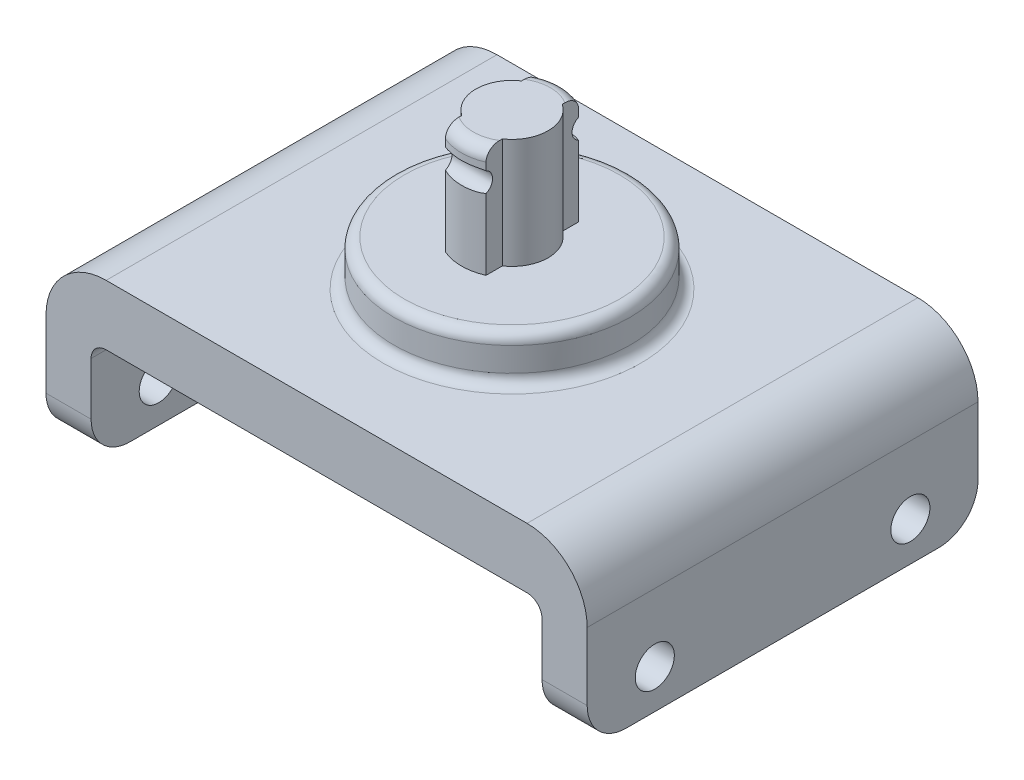
SolidWorks part; units mm, degrees
ref_plane "Front Plane" through (0, 0, 0) normal (0, 0, 1) x (1, 0, 0)
ref_plane "Top Plane" through (0, 0, 0) normal (0, 1, 0) x (1, 0, 0)
ref_plane "Right Plane" through (0, 0, 0) normal (1, 0, 0) x (0, 0, -1)
sketch "Sketch1" plane through (0, 0, 0) normal (0, 0, 1) x (1, 0, 0)
  line L0 (-18, 11.1) -> (18, 11.1)
  line L1 (18, 11.1) -> (18, 0)
  line L2 (18, 0) -> (15, 0)
  line L3 (15, 0) -> (15, 7.1)
  line L4 (15, 7.1) -> (-15, 7.1)
  line L5 (-15, 7.1) -> (-15, 0)
  line L6 (-15, 0) -> (-18, 0)
  line L7 (-18, 0) -> (-18, 11.1)
  line L8 (-15, 0) -> (15, 0) construction
  dimension "D1" = 3
  dimension "D2" = 30
  dimension "D3" = 4
  dimension "D4" = 7.1
extrude "Boss-Extrude1" add sketch "Sketch1" along normal mid plane 26
sketch "Sketch2" plane through (18, 0, 0) normal (1, 0, 0) x (0, 0, -1)
  line L0 (-13, 0) -> (13, 0) construction
  line L1 (-8.5, 2.6) -> (8.5, 2.6) construction
  line L2 (0, 2.6) -> (0, 0) construction
  circle A0 centre (-8.5, 2.6) radius 1.3
  circle A1 centre (8.5, 2.6) radius 1.3
  dimension "D2" = 2.6
  dimension "D1" = 2.6
  dimension "D3" = 17
extrude "Cut-Extrude1" cut sketch "Sketch2" against normal through all
fillet "Fillet1" radius 1 2 edges at (-15, 7.1, 0) (15, 7.1, 0)
fillet "Fillet2" radius 2.6 4 edges at (16.5, 0, 13) (-16.5, 0, 13) (-16.5, 0, -13) (16.5, 0, -13)
fillet "Fillet3" radius 4 2 edges at (18, 11.1, 0) (-18, 11.1, 0)
sketch "Sketch3" plane through (0, 11.1, 0) normal (0, 1, 0) x (1, 0, 0)
  circle A0 centre (0, 0) radius 7.86
  dimension "D1" = 15.72
extrude "Boss-Extrude2" add sketch "Sketch3" along normal blind 3
fillet "Fillet4" radius 0.7 2 edges at (0, 14.1, 7.86) (0, 11.1, -7.86)
sketch "Sketch5" plane through (0, 14.1, 0) normal (0, 1, 0) x (1, 0, 0)
  line L0 (1.35, 1.9904) -> (1.35, 3.0769)
  line L2 (-1.35, -3.0769) -> (-1.35, -1.9904)
  line L4 (1.35, -3.0769) -> (1.35, -1.9904)
  line L7 (-1.35, 1.9904) -> (-1.35, 3.0769)
  arc A0 (-1.35, 1.9904) -> (-1.35, -1.9904) centre (0, 0) ccw
  arc A1 (1.35, -1.9904) -> (1.35, 1.9904) centre (0, 0) ccw
  arc A2 (-1.35, -3.0769) -> (1.35, -3.0769) centre (0, 0) ccw
  arc A3 (1.35, 3.0769) -> (-1.35, 3.0769) centre (0, 0) ccw
  dimension "D1" = 4.81
  dimension "D3" = 6.72
  dimension "D2" = 2.7
extrude "Boss-Extrude3" add sketch "Sketch5" along normal blind 7.32
sketch "Sketch6" plane through (1.35, 0, 0) normal (1, 0, 0) x (0, 0, -1)
  line L0 (-3.36, 21.42) -> (-3.36, 14.1) construction
  line L1 (3.36, 14.1) -> (3.36, 21.42) construction
  line L2 (7.16, 14.1) -> (-7.16, 14.1) construction
  circle A0 centre (-3.36, 19.47) radius 0.715
  circle A1 centre (3.36, 19.47) radius 0.715
  point P8 (-2.645, 19.47)
  point P9 (2.645, 19.47)
  dimension "D1" = 5.29
  dimension "D2" = 5.37
extrude "Cut-Extrude2" cut sketch "Sketch6" against normal through all
fillet "Fillet5" radius 0.8 2 edges at (0, 21.42, -3.36) (0, 21.42, 3.36)
